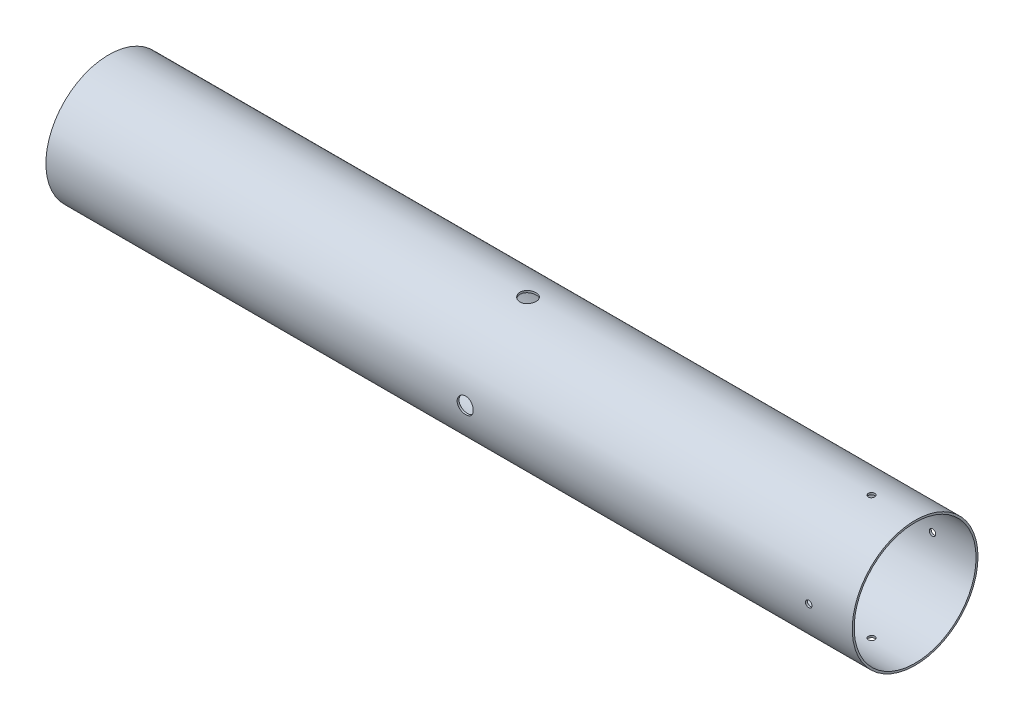
SolidWorks part; units mm, degrees
ref_plane "Alzado" through (0, 0, 0) normal (0, 0, 1) x (1, 0, 0)
ref_plane "Planta" through (0, 0, 0) normal (0, 1, 0) x (1, 0, 0)
ref_plane "Vista lateral" through (0, 0, 0) normal (1, 0, 0) x (0, 0, -1)
sketch "Croquis1" plane through (0, 0, 0) normal (1, 0, 0) x (0, 0, -1)
  circle A0 centre (0, 0) radius 38.99
  circle A1 centre (0, 0) radius 37.79
  dimension "D1" = 75.58
  dimension "D2" = 1.2
  dimension "D3" = 77.98
extrude "Saliente-Extruir1" add sketch "Croquis1" along normal mid plane 500
sketch "Croquis3" plane through (0, 0, 0) normal (0, 0, 1) x (1, 0, 0)
  line L0 (250, 0) -> (70, 0) construction
  line L1 (250, -38.99) -> (250, 38.99) construction
  line L6 (70, 0) -> (10, 0) construction
  circle A0 centre (10, 0) radius 2.4 construction
  circle A1 centre (10, 0) radius 5
  point P8 (70, 0)
  dimension "D3" = 4.8
  dimension "D4" = 10
  dimension "D1" = 180
  dimension "D2" = 60
extrude "Cortar-Extruir1" cut sketch "Croquis3" against normal through all both and the other way through all
pattern_circular "MatrizC4" count 2 over 90 about axis through (250, 0, 0) along (1, 0, 0) of "Cortar-Extruir1"
sketch "Croquis4" plane through (0, 0, 0) normal (0, 0, 1) x (1, 0, 0)
  line L0 (250, -38.99) -> (250, 38.99) construction
  line L1 (223, 0) -> (250, 0) construction
  circle A0 centre (223, 0) radius 2
  dimension "D1" = 27
  dimension "D2" = 4
extrude "Cortar-Extruir2" cut sketch "Croquis4" against normal through all both and the other way through all
pattern_circular "MatrizC5" count 2 over 90 about axis through (250, 0, 0) along (1, 0, 0) of "Cortar-Extruir2"
